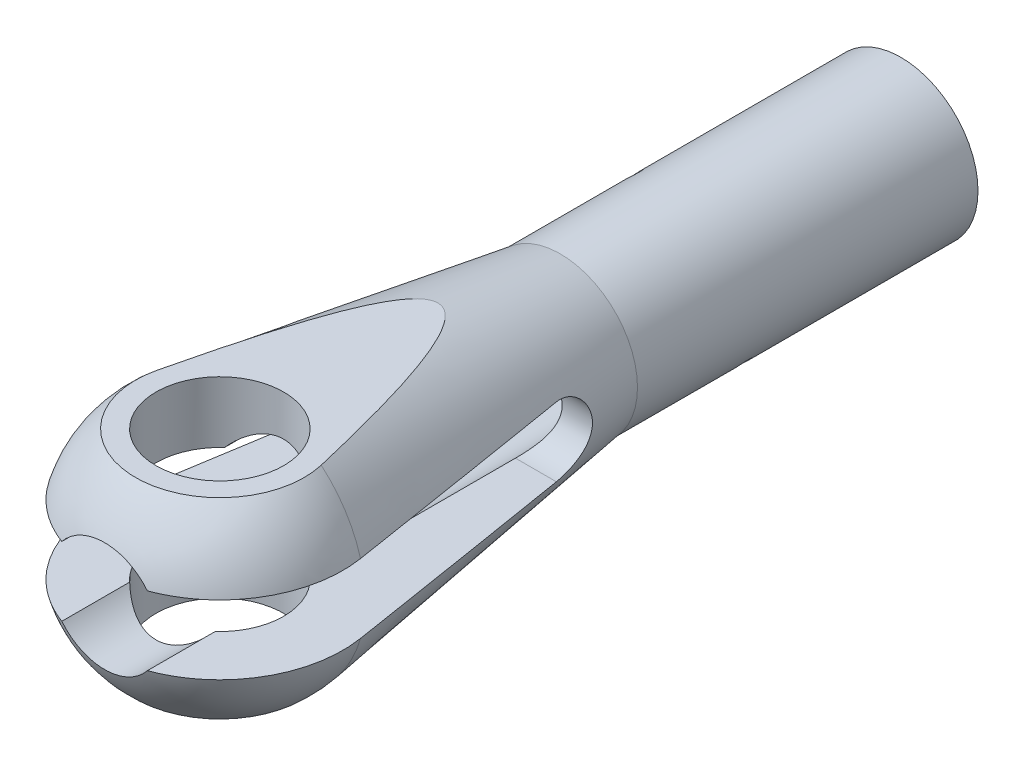
SolidWorks part; units mm, degrees
material "AISI 4340 Steel, normalized"
ref_plane "Front Plane" through (0, 0, 0) normal (0, 0, 1) x (1, 0, 0)
ref_plane "Top Plane" through (0, 0, 0) normal (0, 1, 0) x (1, 0, 0)
ref_plane "Right Plane" through (0, 0, 0) normal (1, 0, 0) x (0, 0, -1)
sketch "Sketch1" plane through (0, 0, 0) normal (1, 0, 0) x (0, 0, -1)
  line L0 (-9.525, 0) -> (50.8, 0)
  line L1 (50.8, 5.7531) -> (25.4, 5.7531)
  line L2 (25.4, 5.7531) -> (1.4392, 9.4156)
  line L3 (50.8, 0) -> (50.8, 5.7531)
  line L4 (50.8, 0) -> (43.5318, 0) construction
  line L5 (-3.0576, 9.525) -> (-12.2265, 9.525) construction
  arc A0 (1.4392, 9.4156) -> (-9.525, 0) centre (0, 0) ccw
  dimension "M_" = 11.5062
  dimension "S/2_" = 9.525
  dimension "B_" = 50.8
  dimension "U_" = 25.4
revolve "Revolve1" add sketch "Sketch1" angle 360 about L0
sketch "Sketch2" plane through (0, 0, -50.8) normal (0, 0, -1) x (-1, 0, 0)
  circle A0 centre (0, 0) radius 3.4544
  dimension "Tap Drill Dia_" = 6.9088
extrude "C-Ext Tap Drill" cut sketch "Sketch2" against normal blind 14.3002
sketch "Sketch3" plane through (0, 0, -36.4998) normal (0, 0, -1) x (-1, 0, 0)
  circle A0 centre (0, 0) radius 4.1021
  dimension "Drill A_" = 8.2042
extrude "C-Ext Rod Clearance Hole" cut sketch "Sketch3" against normal through all
ref_plane "Plane1" through (0, 7.1501, 0) normal (0, 1, 0) x (-1, 0, 0)
sketch "Sketch6" plane through (0, 7.1501, 0) normal (0, 1, 0) x (-1, 0, 0)
  line L0 (-5.7531, -25.4) -> (5.7531, -25.4) construction
  circle A0 centre (0, 0) radius 25.4
extrude "C-Ext Flat" cut sketch "Sketch6" along normal through all
mirror "Mirror Flat" about plane through (0, 0, 0) normal (0, 1, 0) of "C-Ext Flat"
hole_wizard "3/8 (0.375) Diameter Hole1" positions "Sketch8" profile "Sketch7" hole size "3/8" standard "Ansi Inch" end condition through all
sketch "Sketch8" plane through (0, 7.1501, 0) normal (0, 1, 0) x (-1, 0, 0)
  point P0 (0, 0)
sketch "Sketch7" plane through (0, 7.1501, 0) normal (1, 0, 0) x (0, 0, 1)
  line L0 (0, 0) -> (0, 14.3002)
  line L1 (0, 14.3002) -> (4.7625, 14.3002)
  line L2 (4.7625, 14.3002) -> (4.7625, 0)
  line L5 (4.7625, 0) -> (0, 0)
  line L11 (0, -6.35) -> (0, 107.95) construction
  dimension "D_" = 9.525
  dimension "Thru Hole Depth" = 14.3002
sketch "Sketch9" plane through (0, 0, 0) normal (1, 0, 0) x (0, 0, -1)
  line L0 (0, 0) -> (-12.8213, 0) construction
  line L1 (-8.5964, 2.5781) -> (18.8595, 2.5781)
  line L2 (-8.5964, 2.5781) -> (-8.5964, -2.5781)
  line L3 (-8.5964, -2.5781) -> (18.8595, -2.5781)
  line L5 (-8.5964, 4.1021) -> (-8.5964, -4.1021) construction
  arc A0 (18.8595, 2.5781) -> (18.8595, -2.5781) centre (18.8595, 0) cw
  dimension "G_" = 5.1562
  dimension "H_" = 21.4376
extrude "C-Ext Slot" cut sketch "Sketch9" against normal through all and the other way through all
sketch "Sketch13" plane through (0, 0, 0) normal (0, 1, 0) x (1, 0, 0)
  line L1 (4.0767, 49.7417) -> (3.1602, 49.2125)
  line L2 (3.1602, 51.3292) -> (4.0767, 50.8)
  line L3 (3.1602, 50.2708) -> (3.1602, 51.3292) construction
  line L4 (4.0767, 50.8) -> (3.1602, 50.2708)
  line L5 (0, 54.163) -> (0, 48.3921) construction
  line L6 (4.0767, 50.8) -> (2.2436, 50.8) construction
  line L8 (3.1602, 50.2708) -> (4.0767, 49.7417)
  line L9 (4.0767, 48.6833) -> (3.1602, 48.1542)
  line L10 (3.1602, 49.2125) -> (4.0767, 48.6833)
  line L11 (4.0767, 47.625) -> (3.1602, 47.0958)
  line L12 (3.1602, 48.1542) -> (4.0767, 47.625)
  line L13 (4.0767, 46.5667) -> (3.1602, 46.0375)
  line L14 (3.1602, 47.0958) -> (4.0767, 46.5667)
  line L15 (4.0767, 45.5083) -> (3.1602, 44.9792)
  line L16 (3.1602, 46.0375) -> (4.0767, 45.5083)
  line L17 (4.0767, 44.45) -> (3.1602, 43.9208)
  line L18 (3.1602, 44.9792) -> (4.0767, 44.45)
  line L19 (4.0767, 43.3917) -> (3.1602, 42.8625)
  line L20 (3.1602, 43.9208) -> (4.0767, 43.3917)
  line L21 (4.0767, 42.3333) -> (3.1602, 41.8042)
  line L22 (3.1602, 42.8625) -> (4.0767, 42.3333)
  line L23 (4.0767, 41.275) -> (3.1602, 40.7458)
  line L24 (3.1602, 41.8042) -> (4.0767, 41.275)
  line L25 (4.0767, 40.2167) -> (3.1602, 39.6875)
  line L26 (3.1602, 40.7458) -> (4.0767, 40.2167)
  line L27 (4.0767, 39.1583) -> (3.1602, 38.6292)
  line L28 (3.1602, 39.6875) -> (4.0767, 39.1583)
  line L29 (4.0767, 38.1) -> (3.1602, 37.5708)
  line L30 (3.1602, 38.6292) -> (4.0767, 38.1)
  line L31 (4.0767, 37.0417) -> (3.1602, 36.5125)
  line L32 (3.1602, 37.5708) -> (4.0767, 37.0417)
  line L33 (4.0767, 35.9833) -> (3.1602, 35.4542)
  line L34 (3.1602, 36.5125) -> (4.0767, 35.9833)
  line L35 (4.0767, 34.925) -> (3.1602, 34.3958)
  line L36 (3.1602, 35.4542) -> (4.0767, 34.925)
  line L37 (4.0767, 33.8667) -> (3.1602, 33.3375)
  line L38 (3.1602, 34.3958) -> (4.0767, 33.8667)
  line L39 (4.0767, 32.8083) -> (3.1602, 32.2792)
  line L40 (3.1602, 33.3375) -> (4.0767, 32.8083)
  line L41 (4.0767, 31.75) -> (3.1602, 31.2208)
  line L42 (3.1602, 32.2792) -> (4.0767, 31.75)
  line L43 (4.0767, 30.6917) -> (3.1602, 30.1625)
  line L44 (3.1602, 31.2208) -> (4.0767, 30.6917)
  line L45 (4.0767, 29.6333) -> (3.1602, 29.1042)
  line L46 (3.1602, 30.1625) -> (4.0767, 29.6333)
  line L47 (4.0767, 28.575) -> (3.1602, 28.0458)
  line L48 (3.1602, 29.1042) -> (4.0767, 28.575)
  line L49 (4.0767, 27.5167) -> (3.1602, 26.9875)
  line L50 (3.1602, 28.0458) -> (4.0767, 27.5167)
  line L51 (4.0767, 26.4583) -> (3.1602, 25.9292)
  line L52 (3.1602, 26.9875) -> (4.0767, 26.4583)
  line L53 (4.0767, 25.4) -> (3.1602, 24.8708)
  line L54 (3.1602, 25.9292) -> (4.0767, 25.4)
  line L55 (4.0767, 24.3417) -> (3.1602, 23.8125)
  line L56 (3.1602, 24.8708) -> (4.0767, 24.3417)
  line L57 (4.0767, 23.2833) -> (3.1602, 22.7542)
  line L58 (3.1602, 23.8125) -> (4.0767, 23.2833)
  line L59 (4.0767, 22.225) -> (3.1602, 21.6958)
  line L60 (3.1602, 22.7542) -> (4.0767, 22.225)
  line L61 (4.0767, 21.1667) -> (3.1602, 20.6375)
  line L62 (3.1602, 21.6958) -> (4.0767, 21.1667)
  line L63 (4.0767, 20.1083) -> (3.1602, 19.5792)
  line L64 (3.1602, 20.6375) -> (4.0767, 20.1083)
  line L65 (4.0767, 19.05) -> (3.1602, 18.5208)
  line L66 (3.1602, 19.5792) -> (4.0767, 19.05)
  line L67 (4.0767, 17.9917) -> (3.1602, 17.4625)
  line L68 (3.1602, 18.5208) -> (4.0767, 17.9917)
  line L69 (3.1602, 17.4625) -> (2.2436, 17.4625)
  line L70 (2.2436, 17.4625) -> (2.2436, 51.3292)
  line L71 (2.2436, 51.3292) -> (3.1602, 51.3292)
  line L72 (5.7531, 50.8) -> (-5.7531, 50.8) construction
  line L73 (4.1021, 21.4376) -> (4.1021, 36.4998)
  line L74 (-3.3147, 34.925) -> (-3.3147, 15.875)
  line L76 (4.1021, 21.4376) -> (4.1021, 36.4998) construction
  point P15 (3.1602, 50.8)
  dimension "D3" = 0.0254
  dimension "D1" = 60
  dimension "Thread Spacing" = 1.0583
revolve "C-Rev Threads" cut sketch "Sketch13" angle 360 about L5
ref_plane "Plane, Witness Hole" through (0, 0, 0) normal (0.7071, -0.7071, 0) x (0.7071, 0.7071, 0)
sketch "Sketch12" plane through (0, 0, 0) normal (0.7071, -0.7071, 0) x (0.7071, 0.7071, 0)
  line L0 (0, -50.8) -> (0, -25.4) construction
  line L1 (-5.7531, -50.8) -> (5.7531, -50.8) construction
  circle A0 centre (0, -34.925) radius 0.5842
  dimension "D2" = 1.1684
  dimension "Z_" = 15.875
extrude "C-Ext Witness Hole" cut sketch "Sketch12" against normal through all and the other way through all
sketch "Sketch, Hole Center" plane through (0, 0, 0) normal (0, 1, 0) x (1, 0, 0)
  point P0 (0, 0)
